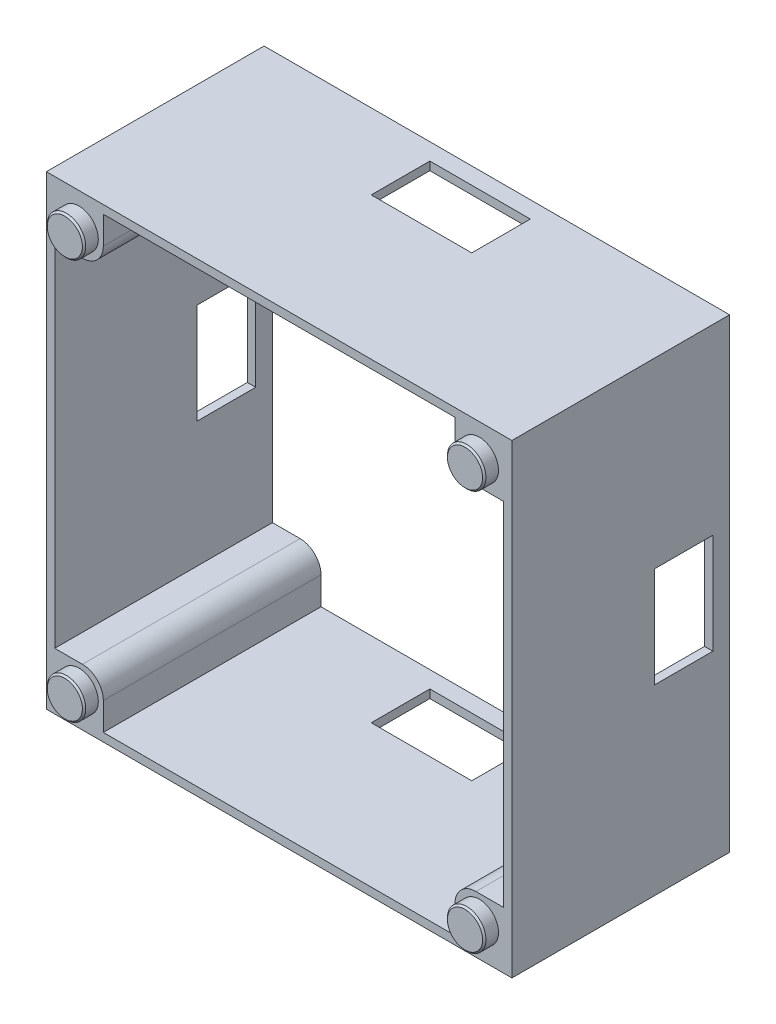
SolidWorks part; units mm, degrees
ref_plane "Přední rovina" through (0, 0, 0) normal (0, 0, 1) x (1, 0, 0)
ref_plane "Horní rovina" through (0, 0, 0) normal (0, 1, 0) x (1, 0, 0)
ref_plane "Pravá rovina" through (0, 0, 0) normal (1, 0, 0) x (0, 0, -1)
sketch "Skica1" plane through (0, 0, 0) normal (0, 0, 1) x (1, 0, 0)
  line L0 (21, -27.8) -> (21, -21)
  line L1 (-27.8, 27.8) -> (27.8, 27.8)
  line L2 (-27.8, 27.8) -> (-27.8, -27.8)
  line L3 (-27.8, -27.8) -> (27.8, -27.8)
  line L4 (27.8, 27.8) -> (27.8, -27.8)
  line L5 (-27.8, 27.8) -> (27.8, -27.8) construction
  line L6 (-27.8, -27.8) -> (27.8, 27.8) construction
  line L7 (-26.8, 26.8) -> (26.8, 26.8)
  line L8 (-26.8, 26.8) -> (-26.8, -26.8)
  line L9 (-26.8, -26.8) -> (26.8, -26.8)
  line L10 (26.8, 26.8) -> (26.8, -26.8)
  line L11 (-26.8, 26.8) -> (26.8, -26.8) construction
  line L12 (-26.8, -26.8) -> (26.8, 26.8) construction
  line L13 (-27.8, 27.8) -> (-21, 27.8)
  line L14 (-27.8, 27.8) -> (-27.8, 21)
  line L15 (-27.8, 21) -> (-21, 21)
  line L16 (-21, 27.8) -> (-21, 21)
  line L17 (27.8, -21) -> (21, -21)
  line L18 (27.8, -27.8) -> (27.8, -21)
  line L19 (27.8, -27.8) -> (21, -27.8)
  line L20 (27.8, 27.8) -> (21, 27.8)
  line L21 (27.8, 27.8) -> (27.8, 21)
  line L22 (27.8, 21) -> (21, 21)
  line L23 (21, 27.8) -> (21, 21)
  line L24 (27.8, -27.8) -> (27.8, -21)
  line L25 (27.8, -27.8) -> (21, -27.8)
  line L26 (21, -27.8) -> (21, -21)
  line L27 (27.8, -21) -> (21, -21)
  line L28 (-27.8, -27.8) -> (-21, -27.8)
  line L29 (-27.8, -27.8) -> (-27.8, -21)
  line L30 (-27.8, -21) -> (-21, -21)
  line L31 (-21, -27.8) -> (-21, -21)
  point P0 (0, 0)
  point P5 (0, 0)
  point P32 (0, 0)
  dimension "D1" = 55.6
  dimension "D2" = 53.6
  dimension "D3" = 6.8
  dimension "D4" = 4
extrude "Přidat vysunutím2" add sketch "Skica1" along normal blind 26 contours L16 L1 L2 L15 L8 L7 | L16 L7 L8 L15 | L1 L23 L7 L10 L22 L4 | L7 L23 L22 L10 | L4 L17 L10 L9 L0 L3 | L10 L17 L0 L9 | L9 L31 L30 L8 | L3 L31 L9 L8 L30 L2 | L2 L30 L8 L15 | L31 L3 L0 L9 | L4 L22 L10 L17 | L23 L1 L16 L7
fillet "Zaoblit1" radius 2.5 4 edges at (-21, -21, 13) (21, -21, 13) (21, 21, 13) (-21, 21, 13)
sketch "Skica2" plane through (0, 0, 0) normal (0, 0, -1) x (-1, 0, 0)
  line L0 (-27.8, 27.8) -> (-27.8, -27.8) construction
  line L1 (27.8, 27.8) -> (-27.8, 27.8) construction
  circle A0 centre (-23.9, 23.9) radius 2.4
  circle A4 centre (23.9, 23.9) radius 2.4
  circle A5 centre (23.9, -23.9) radius 2.4
  circle A6 centre (-23.9, -23.9) radius 2.4
  point P15 (-0.2487, -0.2461)
  point P16 (0, 0)
  dimension "D1" = 4.8
  dimension "D2" = 3.9
  dimension "D3" = 3.9
  dimension "D4" = 4
extrude "Odebrat vysunutím1" cut sketch "Skica2" against normal blind 1.9
sketch "Skica3" plane through (0, 0, 26) normal (0, 0, 1) x (1, 0, 0)
  line L0 (-27.8, 27.8) -> (-27.8, -27.8) construction
  line L1 (-27.8, 27.8) -> (27.8, 27.8) construction
  circle A0 centre (-23.9, 23.9) radius 2.3
  circle A4 centre (23.9, 23.9) radius 2.3
  circle A5 centre (23.9, -23.9) radius 2.3
  circle A6 centre (-23.9, -23.9) radius 2.3
  point P15 (-0.5, 0)
  point P16 (0, 0)
  dimension "D1" = 4.6
  dimension "D2" = 3.9
  dimension "D3" = 3.9
  dimension "D4" = 4
extrude "Přidat vysunutím3" add sketch "Skica3" along normal blind 1.7
chamfer "Zkosení1" distance 0.2 angle 45 4 edges at (-21.6, 23.9, 27.7) (-21.6, -23.9, 27.7) (26.2, -23.9, 27.7) (26.2, 23.9, 27.7)
sketch "Skica4" plane through (0, -27.8, 0) normal (0, -1, 0) x (-1, 0, 0)
  line L0 (27.8, -26) -> (27.8, 0) construction
  line L1 (6, -9) -> (-6, -9)
  line L2 (6, -9) -> (6, -2)
  line L3 (6, -2) -> (-6, -2)
  line L4 (-6, -9) -> (-6, -2)
  line L5 (-27.8, -26) -> (-27.8, 0) construction
  line L6 (27.8, 0) -> (-27.8, 0) construction
  dimension "D1" = 7
  dimension "D2" = 12
  dimension "D3" = 21.8
  dimension "D4" = 21.8
  dimension "D5" = 2
extrude "Odebrat vysunutím2" cut sketch "Skica4" against normal blind 68.7
sketch "Skica5" plane through (-27.8, 0, 0) normal (-1, 0, 0) x (0, 0, 1)
  line L0 (0, 27.8) -> (0, -27.8) construction
  line L1 (2, 6) -> (9, 6)
  line L2 (2, 6) -> (2, -6)
  line L3 (2, -6) -> (9, -6)
  line L4 (9, 6) -> (9, -6)
  line L5 (2, 6) -> (9, -6) construction
  line L6 (2, -6) -> (9, 6) construction
  point P0 (5.5, 0)
  dimension "D1" = 12
  dimension "D2" = 7
  dimension "D3" = 2
extrude "Odebrat vysunutím3" cut sketch "Skica5" against normal blind 55.6
